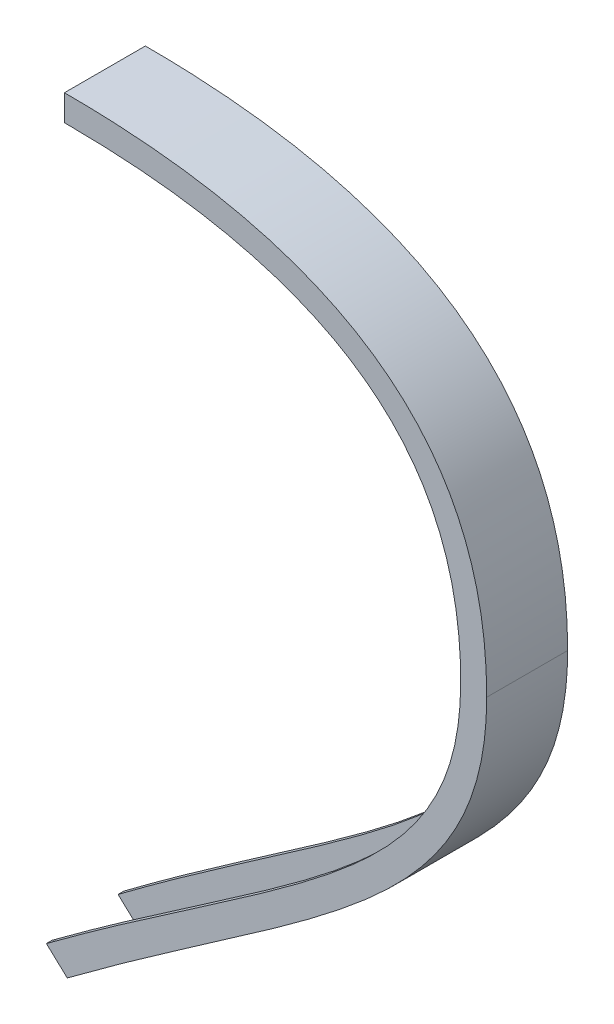
SolidWorks part; units mm, degrees
material "ABS"
ref_plane "Plan de face" through (0, 0, 0) normal (0, 0, 1) x (1, 0, 0)
ref_plane "Plan de dessus" through (0, 0, 0) normal (0, 1, 0) x (1, 0, 0)
ref_plane "Plan de droite" through (0, 0, 0) normal (1, 0, 0) x (0, 0, -1)
sketch "Esquisse1" plane through (0, 0, 0) normal (0, 0, 1) x (1, 0, 0)
  line L0 (-0.004, 119.04) -> (-0.004, 109.04)
  line L5 (-7.4498, -136.9038) -> (-0.004, -143.8218)
  line L11 (-0.004, 129.04) -> (-0.004, 119.04) construction
  line L12 (-0.004, -143.8218) -> (7.322, -150.6284) construction
  line L17 (-10.004, 129.04) -> (-10.004, 108.9145) construction
  line L18 (-15.587, -142.9936) -> (0.5153, -157.9544) construction
  parabola Q2 (145.0949, 12.3477) -> (-0.004, 119.04) focus (94.1746, 49.7897) apex (127.2252, 74.0921)
  spline S0 degree 1 poles (-15.587, -142.9936) (135.0949, 12.3477) knots 0 0 1 1 construction
  spline S1 degree 1 poles (135.0949, 12.3477) (-10.004, 108.9145) knots 0 0 1 1 construction
  spline S2 degree 3 poles (-0.004, -143.8218) (84.0733, -80.8992) (145.0949, -56.5421) (145.0949, 12.3477) knots 0.351934 0.351934 0.351934 0.351934 1 1 1 1
  spline S3 degree 3 poles (-15.587, -142.9936) (-13.2155, -141.2188) (-10.1596, -138.9322) (-6.0729, -135.8731) (-2.9637, -133.5504) (4.8893, -127.7477) (16.8461, -119.1295) (32.0717, -108.4577) (46.5023, -98.4744) (60.0659, -89.0503) (76.8953, -77.0639) (95.3932, -62.8596) (110.0339, -48.9568) (119.2592, -37.6119) (124.9347, -28.8733) (129.3828, -19.7496) (132.0804, -11.6539) (133.6224, -4.7602) (134.463, 0.647) (134.8917, 5.3817) (135.0655, 9.3036) (135.0949, 11.3391) (135.0949, 12.3477) knots 0.327291 0.327291 0.327291 0.327291 0.345571 0.350826 0.358825 0.369336 0.41138 0.453424 0.495469 0.537513 0.579557 0.663646 0.747734 0.789779 0.831823 0.873867 0.915911 0.936934 0.957956 0.978978 0.989489 1 1 1 1 only from (-7.4498, -136.9038) to (135.0949, 12.3477)
  spline S4 degree 3 poles (135.0949, 12.3477) (135.0949, 13.4139) (135.0712, 15.5614) (134.9298, 19.7348) (134.578, 24.8074) (133.8798, 30.6384) (132.5869, 38.0837) (130.303, 46.7758) (126.5229, 56.2654) (121.714, 64.8758) (113.9062, 75.2746) (101.4146, 86.4111) (84.8587, 95.1921) (69.0275, 100.7002) (55.8541, 104.0419) (41.3786, 106.5677) (28.2357, 107.9748) (17.0766, 108.6737) (8.9627, 108.9625) (2.8221, 109.0406) (-1.7514, 109.0406) (-5.4437, 109.0104) (-8.4362, 108.9532) (-10.004, 108.9145) knots 0.497645 0.497645 0.497645 0.497645 0.497754 0.497862 0.498079 0.498296 0.498513 0.498947 0.499381 0.499815 0.500249 0.501117 0.501985 0.502418 0.502852 0.503286 0.50372 0.503937 0.504154 0.504328 0.504382 0.50448 0.504588 0.504588 0.504588 0.504588 only from (135.0949, 12.3477) to (-0.004, 109.04)
  dimension "D1" = 10
extrude "Boss.-Extru.2" add sketch "Esquisse1" along normal blind 2
sketch "Esquisse2" plane through (0, 0, 2) normal (0, 0, 1) x (1, 0, 0)
  line L12 (-7.4498, -136.9038) -> (-0.004, -143.8218) construction
  line L22 (-0.004, 119.04) -> (-0.004, 109.04) construction
  line L23 (-0.004, 120.04) -> (-0.004, 119.04)
  line L24 (-0.004, -143.8218) -> (0.9749, -144.7313)
  parabola Q1 (145.0949, 12.3477) -> (-0.004, 119.04) focus (94.1746, 49.7897) apex (127.2252, 74.0921) construction
  parabola Q2 (145.0949, 12.3477) -> (-0.004, 119.04) focus (94.1746, 49.7897) apex (127.2252, 74.0921)
  spline S1 degree 3 poles (-485.4483, -2049.0757) (-491.2224, 1346.4169) (1202.1307, -1442.3273) (-937.3926, 1692.963) knots -1.089053 -1.089053 -1.089053 -1.089053 2.321166 2.321166 2.321166 2.321166 only from (-0.004, -143.8218) to (145.0949, 12.3477) construction
  spline S2 degree 3 poles (-0.004, -143.8218) (84.0733, -80.8992) (145.0949, -56.5421) (145.0949, 12.3477) knots 0.351934 0.351934 0.351934 0.351934 1 1 1 1
  spline S5 degree 3 poles (0.9749, -144.7313) (1.9403, -144.0095) (4.2169, -142.3136) (9.0692, -138.7326) (15.4868, -134.0622) (23.0357, -128.6584) (32.8956, -121.694) (44.8152, -113.4045) (58.416, -103.9984) (71.2588, -95.0104) (87.2989, -83.4186) (105.1794, -69.3541) (119.7974, -55.0218) (129.3012, -42.8919) (135.2717, -33.3389) (140.0215, -23.2097) (142.9101, -14.1923) (144.5494, -6.5754) (145.4362, -0.6488) (145.884, 4.4861) (146.0642, 8.7055) (146.0944, 10.8763) (146.0944, 11.9543) knots 0.352913 0.352913 0.352913 0.352913 0.36037 0.370523 0.390829 0.411134 0.43144 0.472052 0.512663 0.553274 0.593886 0.675109 0.756331 0.796943 0.837554 0.878166 0.918777 0.939083 0.959389 0.979694 0.989847 1 1 1 1
  spline S7 degree 3 poles (146.0944, 11.9543) (146.0972, 13.072) (146.0788, 15.3199) (145.9458, 19.7153) (145.5993, 25.0903) (144.8945, 31.3277) (143.569, 39.3683) (141.1878, 48.8975) (137.1686, 59.4955) (131.9864, 69.2509) (123.5278, 81.1262) (110.0594, 93.8322) (92.7695, 103.6715) (76.6602, 109.8311) (63.4406, 113.5978) (49.0838, 116.514) (36.1722, 118.2373) (25.2732, 119.1927) (16.816, 119.6977) (9.5257, 119.9425) (3.97, 120.0265) (1.2685, 120.0396) (0.0792, 120.04) (-0.004, 120.04) knots 0.497633 0.497633 0.497633 0.497633 0.497738 0.497844 0.498054 0.498265 0.498476 0.498898 0.499319 0.499741 0.500162 0.501006 0.501849 0.50227 0.502692 0.503114 0.503535 0.503746 0.503957 0.504168 0.504273 0.50435 0.504355 0.504355 0.504355 0.504355
extrude "Boss.-Extru.3" add sketch "Esquisse2" along normal blind 24 and the other way up to surface
sketch "Esquisse3" plane through (0, 0, 26) normal (0, 0, 1) x (1, 0, 0)
  line L16 (-7.4498, -136.9038) -> (0.9749, -144.7313)
  line L18 (-0.004, 120.04) -> (-0.004, 109.04)
  line L22 (-6.2557, -138.0132) -> (0.9749, -144.7313)
  line L23 (-0.004, 120.04) -> (-0.004, 111.0348)
  line L24 (1.996, 111.0348) -> (-0.004, 111.0348)
  line L35 (-4.603, -136.8188) -> (-6.2557, -138.0132)
  spline S3 degree 3 poles (2394.1798, 1663.8382) (-230.6579, -344.959) (-90.7481, -212.3982) (9.0692, -138.7326) (15.4868, -134.0622) (23.0357, -128.6584) (32.8956, -121.694) (44.8152, -113.4045) (58.416, -103.9984) (71.2588, -95.0104) (87.2989, -83.4186) (105.1794, -69.3541) (119.7974, -55.0218) (129.3012, -42.8919) (135.2717, -33.3389) (140.0215, -23.2097) (142.9101, -14.1923) (144.5494, -6.5754) (145.4362, -0.6488) (145.884, 4.4861) (148.3835, 63.0179) (107.9634, 163.1074) (7.6091, -2984.4199) knots -0.389145 -0.389145 -0.389145 -0.389145 0.36037 0.370523 0.390829 0.411134 0.43144 0.472052 0.512663 0.553274 0.593886 0.675109 0.756331 0.796943 0.837554 0.878166 0.918777 0.939083 0.959389 0.979694 0.989847 1.522741 1.522741 1.522741 1.522741 only from (0.9749, -144.7313) to (146.0944, 11.9543)
  spline S4 degree 3 poles (73.7854, -985.734) (119.6896, 101.2844) (136.5323, 42.4043) (134.8917, 5.3817) (134.463, 0.647) (133.6224, -4.7602) (132.0804, -11.6539) (129.3828, -19.7496) (124.9347, -28.8733) (119.2592, -37.6119) (110.0339, -48.9568) (95.3932, -62.8596) (76.8953, -77.0639) (60.0659, -89.0503) (46.5023, -98.4744) (32.0717, -108.4577) (16.8461, -119.1295) (4.8893, -127.7477) (-2.9637, -133.5504) (-49.5282, -168.3351) (-83.634, -195.6095) (-861.1741, -657.5605) knots -0.027558 -0.027558 -0.027558 -0.027558 0.337802 0.348314 0.369336 0.390358 0.41138 0.453424 0.495469 0.537513 0.579557 0.663646 0.747734 0.789779 0.831823 0.873867 0.915911 0.957956 0.968467 0.976465 1.313868 1.313868 1.313868 1.313868 only from (135.0949, 12.3477) to (-7.4498, -136.9038)
  spline S5 degree 3 poles (991.9678, -17.3747) (-305.2292, 57.7541) (-109.8016, 110.4736) (8.9627, 108.9625) (17.0766, 108.6737) (28.2357, 107.9748) (41.3786, 106.5677) (55.8541, 104.0419) (69.0275, 100.7002) (84.8587, 95.1921) (101.4146, 86.4111) (113.9062, 75.2746) (121.714, 64.8758) (126.5229, 56.2654) (130.303, 46.7758) (132.5869, 38.0837) (133.8798, 30.6384) (134.578, 24.8074) (134.9298, 19.7348) (136.3543, -22.3098) (120.4651, -84.55) (84.4646, 1010.9657) knots 0.489687 0.489687 0.489687 0.489687 0.497905 0.498079 0.498296 0.498513 0.498947 0.499381 0.499815 0.500249 0.501117 0.501985 0.502418 0.502852 0.503286 0.50372 0.503937 0.504154 0.504371 0.50448 0.508526 0.508526 0.508526 0.508526 only from (-0.004, 109.04) to (135.0949, 12.3477)
  spline S6 degree 3 poles (0.9749, -144.7313) (1.9403, -144.0095) (4.2169, -142.3136) (9.0692, -138.7326) (15.4868, -134.0622) (23.0357, -128.6584) (32.8956, -121.694) (44.8152, -113.4045) (58.416, -103.9984) (71.2588, -95.0104) (87.2989, -83.4186) (105.1794, -69.3541) (119.7974, -55.0218) (129.3012, -42.8919) (135.2717, -33.3389) (140.0215, -23.2097) (142.9101, -14.1923) (144.5494, -6.5754) (145.4362, -0.6488) (145.884, 4.4861) (146.0642, 8.7055) (146.0944, 10.8763) (146.0944, 11.9543) knots 0.352913 0.352913 0.352913 0.352913 0.36037 0.370523 0.390829 0.411134 0.43144 0.472052 0.512663 0.553274 0.593886 0.675109 0.756331 0.796943 0.837554 0.878166 0.918777 0.939083 0.959389 0.979694 0.989847 1 1 1 1
  spline S8 degree 3 poles (46.0092, 3009.8889) (110.741, -148.5479) (147.907, -45.1095) (145.9458, 19.7153) (145.5993, 25.0903) (144.8945, 31.3277) (143.569, 39.3683) (141.1878, 48.8975) (137.1686, 59.4955) (131.9864, 69.2509) (123.5278, 81.1262) (110.0594, 93.8322) (92.7695, 103.6715) (76.6602, 109.8311) (63.4406, 113.5978) (49.0838, 116.514) (36.1722, 118.2373) (25.2732, 119.1927) (16.816, 119.6977) (9.5257, 119.9425) (3.97, 120.0265) (-29.2686, 120.1876) (-64.0501, 116.4969) (-2999.4289, 102.0798) knots 0.491837 0.491837 0.491837 0.491837 0.497738 0.497844 0.498054 0.498265 0.498476 0.498898 0.499319 0.499741 0.500162 0.501006 0.501849 0.50227 0.502692 0.503114 0.503535 0.503746 0.503957 0.504168 0.504273 0.50435 0.506478 0.506478 0.506478 0.506478 only from (146.0944, 11.9543) to (-0.004, 120.04)
  spline S9 degree 3 poles (146.0944, 11.9543) (146.0972, 13.072) (146.0788, 15.3199) (145.9458, 19.7153) (145.5993, 25.0903) (144.8945, 31.3277) (143.569, 39.3683) (141.1878, 48.8975) (137.1686, 59.4955) (131.9864, 69.2509) (123.5278, 81.1262) (110.0594, 93.8322) (92.7695, 103.6715) (76.6602, 109.8311) (63.4406, 113.5978) (49.0838, 116.514) (36.1722, 118.2373) (25.2732, 119.1927) (16.816, 119.6977) (9.5257, 119.9425) (3.97, 120.0265) (1.2685, 120.0396) (0.0792, 120.04) (-0.004, 120.04) knots 0.497633 0.497633 0.497633 0.497633 0.497738 0.497844 0.498054 0.498265 0.498476 0.498898 0.499319 0.499741 0.500162 0.501006 0.501849 0.50227 0.502692 0.503114 0.503535 0.503746 0.503957 0.504168 0.504273 0.50435 0.504355 0.504355 0.504355 0.504355
  spline S11 degree 3 poles (1.996, 111.0348) (3.4493, 111.0272) (6.3735, 110.9949) (12.079, 110.8631) (19.0414, 110.572) (27.0966, 110.0219) (37.4441, 109.0223) (49.6368, 107.277) (63.0773, 104.4032) (75.3258, 100.7671) (90.0703, 94.9297) (105.558, 85.8383) (117.3268, 74.4436) (124.6924, 63.8711) (129.2186, 55.1594) (132.7553, 45.6198) (134.8686, 36.9425) (136.0486, 29.5549) (136.673, 23.7803) (137.0425, 17.8013) (137.0949, 13.6147) (137.0949, 11.546) knots 0.497925 0.497925 0.497925 0.497925 0.49803 0.498135 0.498344 0.498553 0.498762 0.49918 0.499598 0.500016 0.500434 0.50127 0.502107 0.502525 0.502943 0.503361 0.503779 0.503988 0.504197 0.504406 0.504615 0.504615 0.504615 0.504615
  spline S12 degree 3 poles (137.0949, 11.546) (137.0905, 10.56) (137.054, 8.5722) (136.8731, 4.7265) (136.4481, 0.0786) (135.6295, -5.2513) (134.1385, -12.0599) (131.5433, -20.0763) (127.2872, -29.0989) (121.8897, -37.7007) (113.1692, -48.7949) (99.4234, -62.2431) (82.136, -75.7729) (66.4153, -87.0516) (53.7429, -95.8461) (40.2519, -105.0892) (28.3791, -113.2609) (18.534, -120.1385) (10.9866, -125.4804) (4.5616, -130.1014) (-0.6485, -133.899) (-3.2899, -135.8468) (-4.603, -136.8188) knots 0.327291 0.327291 0.327291 0.327291 0.337399 0.347506 0.367721 0.387937 0.408152 0.448582 0.489012 0.529442 0.569872 0.650732 0.731592 0.772022 0.812452 0.852882 0.893312 0.913527 0.933742 0.953957 0.964065 0.974172 0.974172 0.974172 0.974172
  dimension "D1" = 0
extrude "Boss.-Extru.4" add sketch "Esquisse3" along normal blind 2
